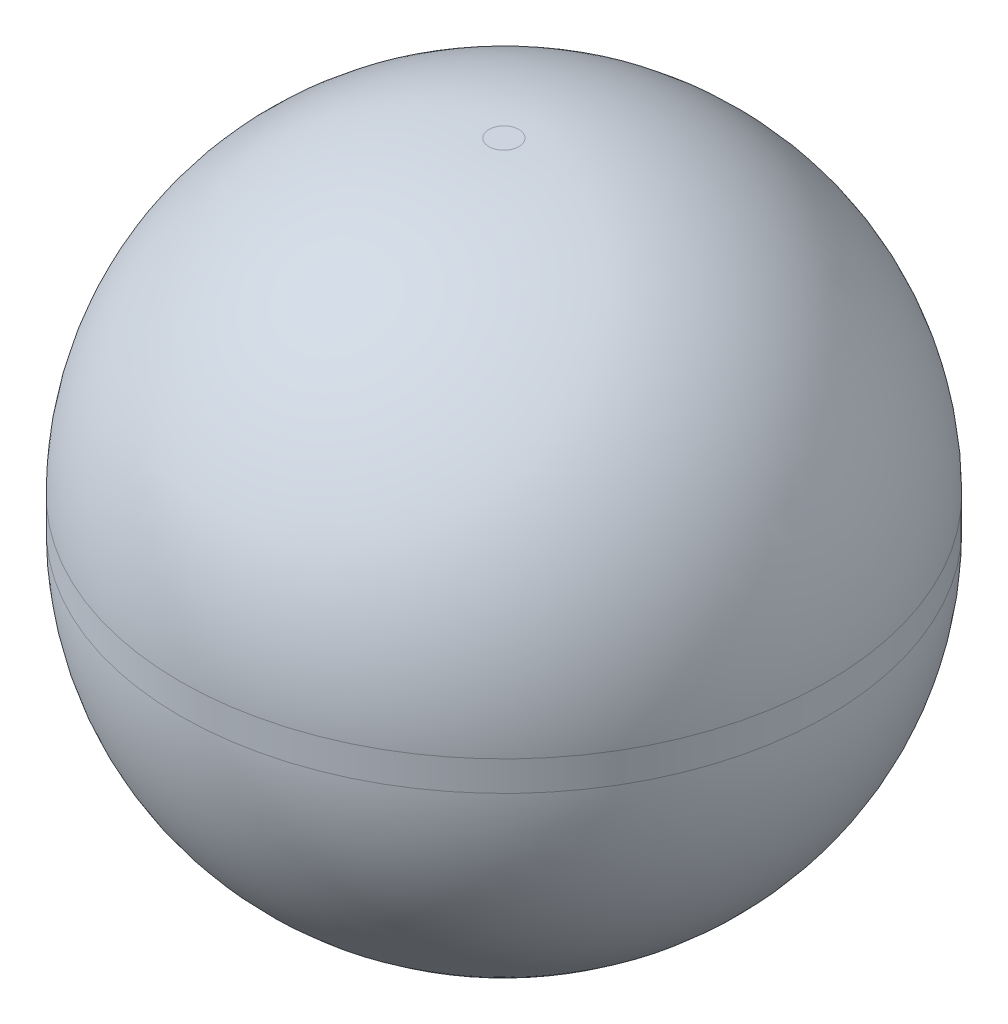
SolidWorks part; units mm, degrees
ref_plane "Plan de face" through (0, 0, 0) normal (0, 0, 1) x (1, 0, 0)
ref_plane "Plan de dessus" through (0, 0, 0) normal (0, 1, 0) x (1, 0, 0)
ref_plane "Plan de droite" through (0, 0, 0) normal (1, 0, 0) x (0, 0, -1)
sketch "Esquisse1" plane through (0, 0, 0) normal (0, 1, 0) x (1, 0, 0)
  circle A0 centre (0, 0) radius 32.5
  dimension "D1" = 65
extrude "Extrusion1" add sketch "Esquisse1" along normal blind 65
fillet "Congé1" radius 31 2 edges at (0, 0, 32.5) (0, 65, 32.5)
